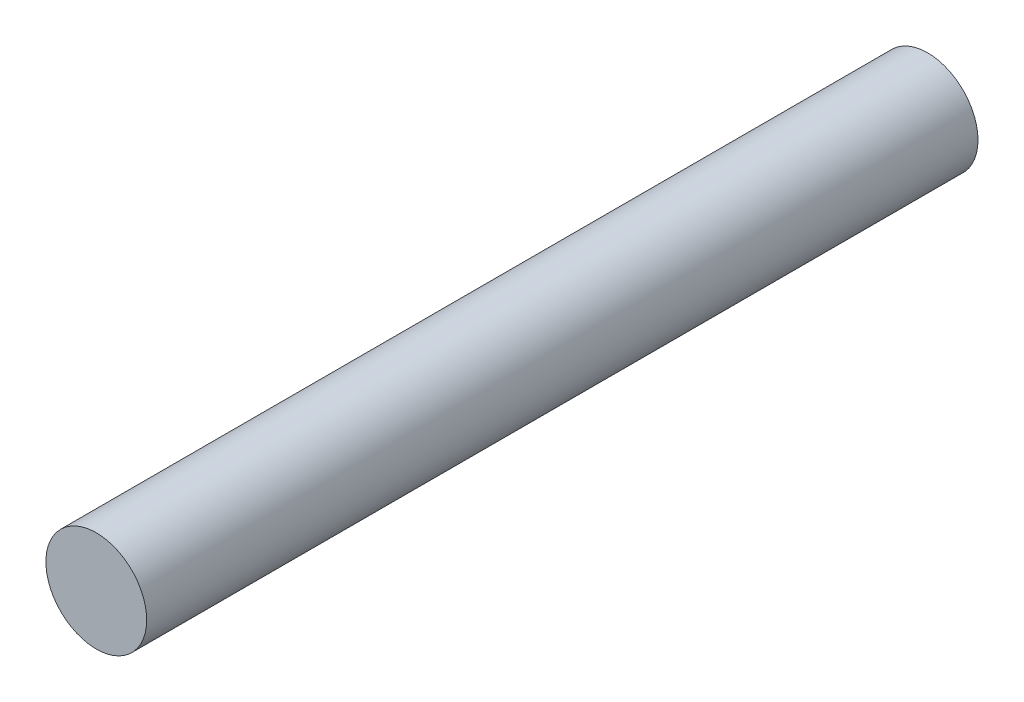
SolidWorks part; units mm, degrees
ref_plane "Front Plane" through (0, 0, 0) normal (0, 0, 1) x (1, 0, 0)
ref_plane "Top Plane" through (0, 0, 0) normal (0, 1, 0) x (1, 0, 0)
ref_plane "Right Plane" through (0, 0, 0) normal (1, 0, 0) x (0, 0, -1)
sketch "Sketch1" plane through (0, 0, 0) normal (0, 0, 1) x (1, 0, 0)
  circle A0 centre (0, 0) radius 4
  dimension "D1" = 8
extrude "Boss-Extrude1" add sketch "Sketch1" along normal blind 66
